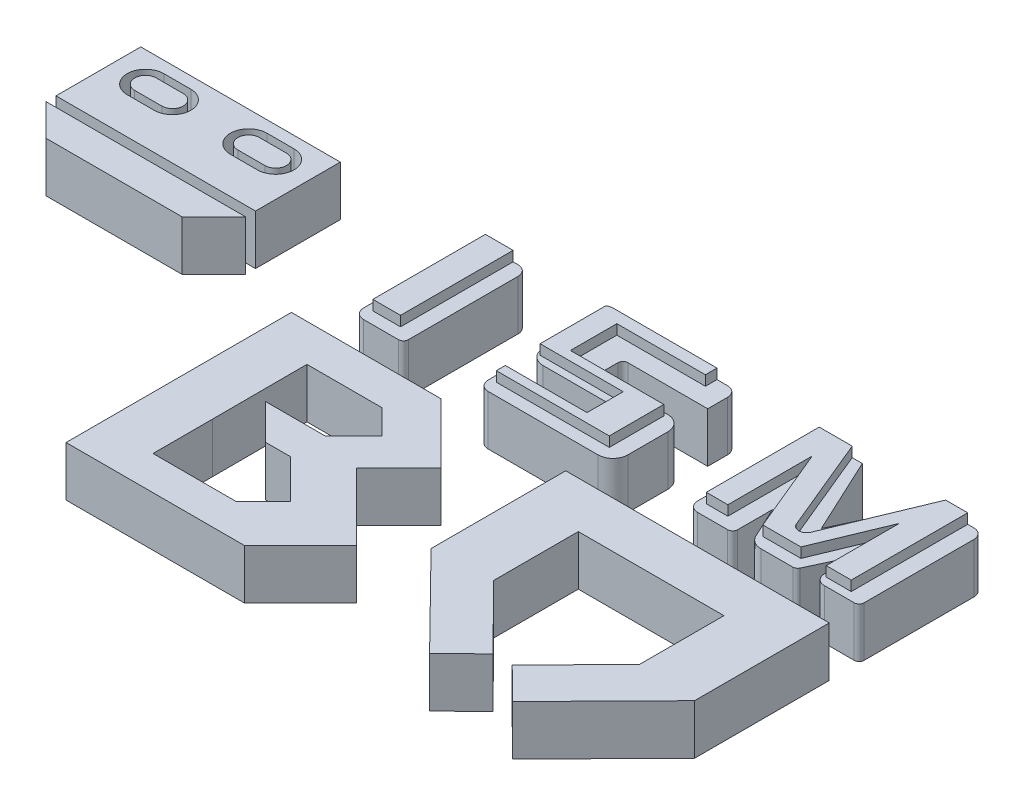
SolidWorks part; units mm, degrees
ref_plane "Front Plane" through (0, 0, 0) normal (0, 0, 1) x (1, 0, 0)
ref_plane "Top Plane" through (0, 0, 0) normal (0, 1, 0) x (1, 0, 0)
ref_plane "Right Plane" through (0, 0, 0) normal (1, 0, 0) x (0, 0, -1)
sketch "Sketch2" plane through (0, 0, 0) normal (0, 1, 0) x (1, 0, 0)
  line L0 (-27.2307, 23.643) -> (-27.2307, -21.537)
  line L1 (-27.2307, 23.643) -> (2.7693, 23.643)
  line L2 (2.7693, 23.643) -> (14.792, 11.6241)
  line L3 (14.792, 11.6241) -> (6.3081, 3.1375)
  line L4 (6.3081, 3.1375) -> (19.7452, -10.2954)
  line L5 (19.7452, -10.2954) -> (8.5072, -21.537)
  line L6 (8.5072, -21.537) -> (-27.2307, -21.537)
  line L7 (2.7693, 23.643) -> (27.7693, 23.643) construction
  line L8 (27.7693, 23.643) -> (80.5993, 23.643)
  line L9 (80.5993, 23.643) -> (80.5993, -3.357)
  line L10 (-16.608, -2.7969) -> (-16.652, 16.1779)
  line L11 (-16.608, -2.7969) -> (-16.608, -14.7294)
  line L12 (-16.652, 16.1779) -> (-1.652, 16.1779)
  line L13 (-1.652, 16.1779) -> (3.2978, 11.2282)
  line L14 (3.2978, 11.2282) -> (-2.3591, 5.5713)
  line L15 (-2.3591, 5.5713) -> (-14.3591, 5.5713)
  line L16 (-14.3591, 5.5713) -> (-7.288, -1.4997)
  line L17 (-7.288, -1.4997) -> (-2.288, -1.4997)
  line L18 (-2.288, -1.4997) -> (5.4902, -9.2779)
  line L19 (5.4902, -9.2779) -> (0.0386, -14.7294)
  line L20 (0.0386, -14.7294) -> (-16.608, -14.7294)
  line L21 (80.5993, -3.357) -> (62.5157, -21.7369)
  line L22 (62.5157, -21.7369) -> (56.1002, -15.4248)
  line L23 (56.1002, -15.4248) -> (68.7843, -2.6532)
  line L24 (68.7843, -2.6532) -> (68.7843, 14.3468)
  line L25 (68.7843, 14.3468) -> (39.5843, 14.3468)
  line L26 (54.1843, 23.643) -> (54.1843, 14.3468) construction
  line L27 (27.7693, 23.643) -> (27.7693, -3.357)
  line L28 (27.7693, -3.357) -> (45.8529, -21.7369)
  line L29 (45.8529, -21.7369) -> (52.2684, -15.4248)
  line L30 (52.2684, -15.4248) -> (39.5843, -2.6532)
  line L31 (39.5843, -2.6532) -> (39.5843, 14.3468)
  line L32 (80.5993, 23.643) -> (80.5993, 29.643) construction
  line L33 (80.5993, 29.643) -> (80.5993, 54.643)
  line L34 (80.5993, 54.643) -> (70.5993, 54.643)
  line L35 (70.5993, 54.643) -> (63.4148, 39.2358)
  line L36 (80.5993, 29.643) -> (71.5993, 29.643)
  line L37 (71.5993, 29.643) -> (71.5993, 37.643)
  line L38 (71.5993, 37.643) -> (67.886, 29.6797)
  line L39 (63.4148, 29.6797) -> (63.386, 29.6797)
  line L40 (63.4148, 39.2358) -> (63.4148, 27.3074) construction
  line L41 (67.886, 29.6797) -> (58.9436, 29.6797)
  line L42 (55.2303, 37.643) -> (58.9436, 29.6797)
  line L43 (55.2303, 29.643) -> (55.2303, 37.643)
  line L44 (46.2303, 29.643) -> (55.2303, 29.643)
  line L45 (46.2303, 29.643) -> (46.2303, 54.643)
  line L46 (46.2303, 54.643) -> (56.2303, 54.643)
  line L47 (56.2303, 54.643) -> (63.4148, 39.2358)
  line L48 (46.2303, 54.643) -> (31.2303, 54.643) construction
  line L49 (31.2303, 54.643) -> (4.2303, 54.643)
  line L50 (4.2303, 54.643) -> (4.2303, 39.643)
  line L51 (4.2303, 39.643) -> (21.2303, 39.643)
  line L52 (21.2303, 39.643) -> (21.2303, 34.643)
  line L53 (21.2303, 34.643) -> (4.2303, 34.643)
  line L57 (31.2303, 43.643) -> (14.2303, 43.643)
  line L58 (14.2303, 43.643) -> (14.2303, 48.643)
  line L59 (14.2303, 48.643) -> (31.2303, 48.643)
  line L60 (31.2303, 48.643) -> (31.2303, 54.643)
  line L61 (4.2303, 34.643) -> (4.2303, 29.643)
  line L62 (4.2303, 29.643) -> (31.2303, 29.643)
  line L63 (31.2303, 29.643) -> (31.2303, 43.643)
  line L64 (4.2303, 54.643) -> (-10.7697, 54.643) construction
  line L65 (-10.7697, 54.643) -> (-10.7697, 29.643)
  line L66 (-10.7697, 29.643) -> (-20.7697, 29.643)
  line L67 (-20.7697, 29.643) -> (-20.7697, 54.643)
  line L68 (-20.7697, 54.643) -> (-10.7697, 54.643)
  line L70 (-48.4316, 54.643) -> (-48.4316, 37.643)
  line L71 (-48.4316, 54.643) -> (-88.4316, 54.643)
  line L72 (-88.4316, 54.643) -> (-88.4316, 37.643)
  line L73 (-88.4316, 37.643) -> (-48.4316, 37.643)
  line L74 (-60.4111, 37.643) -> (-60.4111, 35.643) construction
  line L75 (-88.4316, 35.643) -> (-48.4316, 35.643)
  line L76 (-48.4316, 35.643) -> (-54.7955, 29.2791)
  line L77 (-68.4316, 35.643) -> (-68.4316, 41.2952) construction
  line L78 (-88.4316, 35.643) -> (-82.0676, 29.2791)
  line L79 (-82.0676, 29.2791) -> (-54.7955, 29.2791)
  line L80 (-81.4838, 48.643) -> (-76.0649, 48.643) construction
  line L81 (-81.4838, 50.8024) -> (-76.0649, 50.8024)
  line L82 (-81.4838, 46.4836) -> (-76.0649, 46.4836)
  line L83 (-55.3793, 48.643) -> (-60.7983, 48.643) construction
  line L84 (-55.3793, 50.8024) -> (-60.7983, 50.8024)
  line L85 (-55.3793, 46.4836) -> (-60.7983, 46.4836)
  line L86 (-81.4838, 48.643) -> (-76.0649, 48.643) construction
  line L87 (-81.4838, 52.3109) -> (-76.0649, 52.3109)
  line L88 (-81.4838, 44.9751) -> (-76.0649, 44.9751)
  line L89 (-55.3793, 48.643) -> (-60.7983, 48.643) construction
  line L90 (-55.3793, 52.3109) -> (-60.7983, 52.3109)
  line L91 (-55.3793, 44.9751) -> (-60.7983, 44.9751)
  arc A0 (-81.4838, 50.8024) -> (-81.4838, 46.4836) centre (-81.4838, 48.643) ccw
  arc A1 (-76.0649, 46.4836) -> (-76.0649, 50.8024) centre (-76.0649, 48.643) ccw
  arc A2 (-55.3793, 50.8024) -> (-55.3793, 46.4836) centre (-55.3793, 48.643) cw
  arc A3 (-60.7983, 46.4836) -> (-60.7983, 50.8024) centre (-60.7983, 48.643) cw
  arc A4 (-81.4838, 52.3109) -> (-81.4838, 44.9751) centre (-81.4838, 48.643) ccw
  arc A5 (-76.0649, 44.9751) -> (-76.0649, 52.3109) centre (-76.0649, 48.643) ccw
  arc A6 (-55.3793, 52.3109) -> (-55.3793, 44.9751) centre (-55.3793, 48.643) cw
  arc A7 (-60.7983, 44.9751) -> (-60.7983, 52.3109) centre (-60.7983, 48.643) cw
  point P34 (54.1843, 14.3468)
  point P81 (-78.7743, 48.643)
  point P88 (-58.0888, 48.643)
  point P95 (-78.7743, 48.643)
  point P102 (-58.0888, 48.643)
  dimension "D1" = 45.18
  dimension "D2" = 30
  dimension "D3" = 17
  dimension "D4" = 12
  dimension "D5" = 19
  dimension "D6" = 25
  dimension "D7" = 52.83
  dimension "D8" = 15
  dimension "D9" = 7
  dimension "D10" = 8
  dimension "D11" = 12
  dimension "D12" = 10
  dimension "D13" = 5
  dimension "D14" = 11
  dimension "D15" = 27
  dimension "D16" = 9
  dimension "D17" = 18
  dimension "D18" = 17
  dimension "D19" = 14.6
  dimension "D20" = 6
  dimension "D21" = 25
  dimension "D22" = 10
  dimension "D23" = 17
  dimension "D24" = 115
  dimension "D25" = 9
  dimension "D26" = 8
  dimension "D27" = 25
  dimension "D28" = 4.5
  dimension "D29" = 15
  dimension "D30" = 27
  dimension "D31" = 15
  dimension "D32" = 17
  dimension "D33" = 5
  dimension "D34" = 15
  dimension "D35" = 10
  dimension "D36" = 17
  dimension "D37" = 5
  dimension "D39" = 40
  dimension "D40" = 2
  dimension "D41" = 9
extrude "Boss-Extrude1" add sketch "Sketch2" along normal blind 10 contours L6 L5 L4 L3 L2 L1 L0 L19 L20 L11 L10 L12 L13 L14 L15 L16 L17 L18 | L30 L31 L25 L24 L23 L22 L21 L9 L8 L27 L28 L29 | L47 L46 L45 L44 L43 L42 L41 L39 L38 L37 L36 L33 L34 L35 | L62 L63 L57 L58 L59 L60 L49 L50 L51 L52 L53 L61 | L68 L67 L66 L65 | L78 L79 L76 L75 | L72 L73 L70 L71 A5 L88 A4 L87 L91 A7 L90 A6 | L82 A1 L81 A0 | A3 L85 A2 L84
sketch "Sketch3" plane through (0, 10, 0) normal (0, 1, 0) x (1, 0, 0)
  line L0 (-19.3357, 54.643) -> (-19.3357, 32.0698)
  line L1 (-20.7697, 54.643) -> (-10.7697, 54.643) construction
  line L2 (-19.3357, 32.0698) -> (-13.7828, 32.0698)
  line L3 (-13.7828, 32.0698) -> (-13.7828, 54.643)
  line L4 (-13.7828, 54.643) -> (-19.3357, 54.643)
extrude "Boss-Extrude2" add sketch "Sketch3" along normal blind 2
sketch "Sketch4" plane through (0, 10, 0) normal (0, 1, 0) x (1, 0, 0)
  line L0 (27.0971, 54.643) -> (27.0971, 52.3136)
  line L1 (31.2303, 54.643) -> (4.2303, 54.643) construction
  line L2 (27.0971, 52.3136) -> (9.3478, 52.3136)
  line L3 (9.3478, 52.3136) -> (9.3478, 42.9977)
  line L4 (9.3478, 42.9977) -> (28.0777, 42.9977)
  line L5 (28.0777, 42.9977) -> (28.0777, 32.0637)
  line L6 (28.0777, 32.0637) -> (5.4253, 32.0637)
  line L7 (5.4253, 32.0637) -> (5.4253, 33.8779)
  line L8 (5.4253, 33.8779) -> (21.8017, 33.8779)
  line L9 (21.8017, 33.8779) -> (21.8017, 41.1345)
  line L10 (21.8017, 41.1345) -> (5.1312, 41.1345)
  line L11 (5.1312, 41.1345) -> (5.1312, 54.643)
  line L12 (5.1312, 54.643) -> (27.0971, 54.643)
extrude "Boss-Extrude3" add sketch "Sketch4" along normal blind 2
sketch "Sketch5" plane through (0, 10, 0) normal (0, 1, 0) x (1, 0, 0)
  line L0 (47.5898, 31.9994) -> (47.5898, 54.643)
  line L1 (46.2303, 54.643) -> (56.2303, 54.643) construction
  line L2 (47.5898, 54.643) -> (54.206, 54.643)
  line L3 (54.206, 54.643) -> (62.1219, 35.5438)
  line L4 (65.0165, 35.5438) -> (72.9324, 54.643)
  line L5 (80.5993, 54.643) -> (70.5993, 54.643) construction
  line L6 (72.9324, 54.643) -> (77.3629, 54.643)
  line L7 (77.3629, 54.643) -> (77.3629, 31.2905)
  line L8 (77.3629, 31.2905) -> (72.3416, 31.2905)
  line L9 (72.3416, 31.2905) -> (72.3416, 45.9407)
  line L10 (72.3416, 45.9407) -> (66.5635, 31.9994)
  line L11 (66.5635, 31.9994) -> (58.9319, 31.9994)
  line L12 (58.9319, 31.9994) -> (51.9118, 48.9373)
  line L13 (51.9118, 48.9373) -> (51.9118, 31.9994)
  line L14 (51.9118, 31.9994) -> (47.5898, 31.9994)
  arc A0 (62.1219, 35.5438) -> (65.0165, 35.5438) centre (63.5692, 36.1436) ccw
extrude "Boss-Extrude4" add sketch "Sketch5" along normal blind 2
fillet "Fillet1" radius 3 2 edges at (31.2303, 5, -29.643) (31.2303, 5, -43.643)
fillet "Fillet2" radius 2 3 edges at (4.2303, 5, -54.643) (4.2303, 5, -29.643) (31.2303, 5, -54.643)
fillet "Fillet3" radius 3 1 edges at (4.2303, 5, -39.643)
fillet "Fillet4" radius 1 4 edges at (21.2303, 5, -34.643) (21.2303, 5, -39.643) (14.2303, 5, -43.643) (14.2303, 5, -48.643)
fillet "Fillet5" radius 3 1 edges at (58.9436, 5, -29.6797)
fillet "Fillet6" radius 2 3 edges at (80.5993, 5, -54.643) (71.5993, 5, -29.643) (46.2303, 5, -29.643)
fillet "Fillet7" radius 1 4 edges at (80.5993, 5, -29.643) (67.886, 5, -29.6797) (55.2303, 5, -29.643) (46.2303, 5, -54.643)
fillet "Fillet8" radius 2 1 edges at (-20.7697, 5, -29.643)
fillet "Fillet9" radius 2 1 edges at (-10.7697, 5, -54.643)
fillet "Fillet10" radius 1 2 edges at (-10.7697, 5, -29.643) (-20.7697, 5, -54.643)
